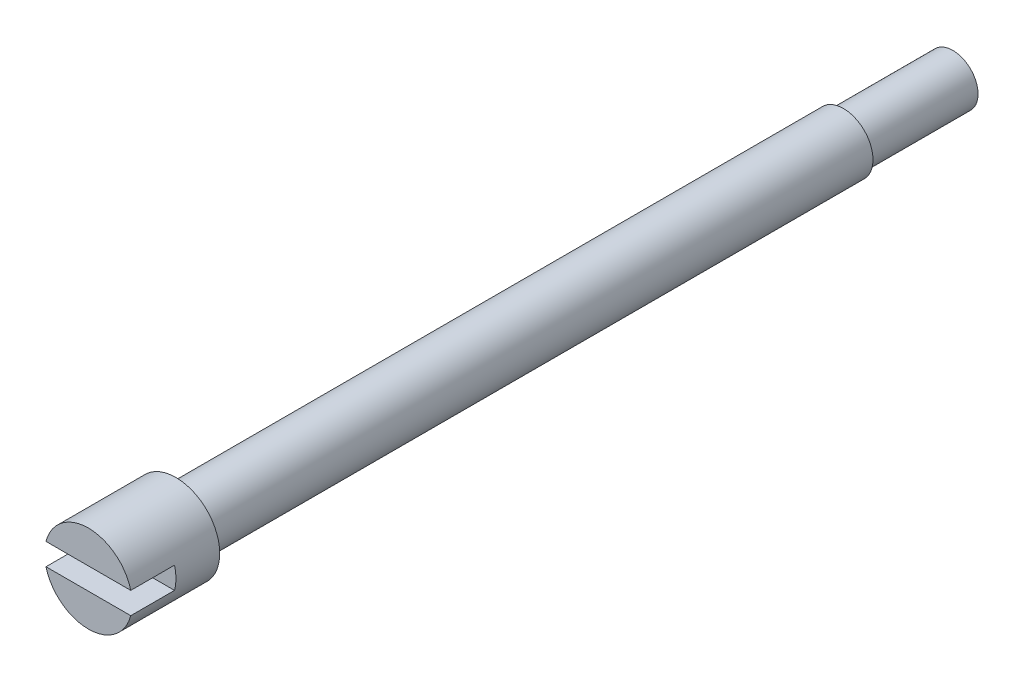
SolidWorks part; units mm, degrees
ref_plane "Front Plane" through (0, 0, 0) normal (0, 0, 1) x (1, 0, 0)
ref_plane "Top Plane" through (0, 0, 0) normal (0, 1, 0) x (1, 0, 0)
ref_plane "Right Plane" through (0, 0, 0) normal (1, 0, 0) x (0, 0, -1)
sketch "Sketch1" plane through (0, 0, 0) normal (0, 0, 1) x (1, 0, 0)
  circle A0 centre (0, 0) radius 1.35
  dimension "D1" = 2.7
extrude "Boss-Extrude1" add sketch "Sketch1" along normal blind 35.5
sketch "Sketch2" plane through (0, 0, 35.5) normal (0, 0, 1) x (1, 0, 0)
  circle A0 centre (0, 0) radius 2
  circle A1 centre (0, 0) radius 1.35 construction
  dimension "D1" = 4
extrude "Boss-Extrude2" add sketch "Sketch2" along normal blind 4
sketch "Sketch3" plane through (0, 0, 39.5) normal (0, 0, 1) x (1, 0, 0)
  line L0 (-2, 0) -> (2, 0) construction
  line L1 (2, -0.5) -> (-2, -0.5)
  line L3 (2, -0.5) -> (2, 0.5)
  line L4 (2, 0.5) -> (-2, 0.5)
  line L5 (-2, -0.5) -> (-2, 0.5)
  circle A0 centre (0, 0) radius 2 construction
  dimension "D1" = 1
extrude "Cut-Extrude1" cut sketch "Sketch3" against normal blind 2
sketch "Sketch4" plane through (0, 0, 0) normal (0, 0, -1) x (-1, 0, 0)
  circle A0 centre (0, 0) radius 1.15
  dimension "D1" = 2.3
extrude "Cut-Extrude2" cut sketch "Sketch4" against normal blind 5 flip side to cut
